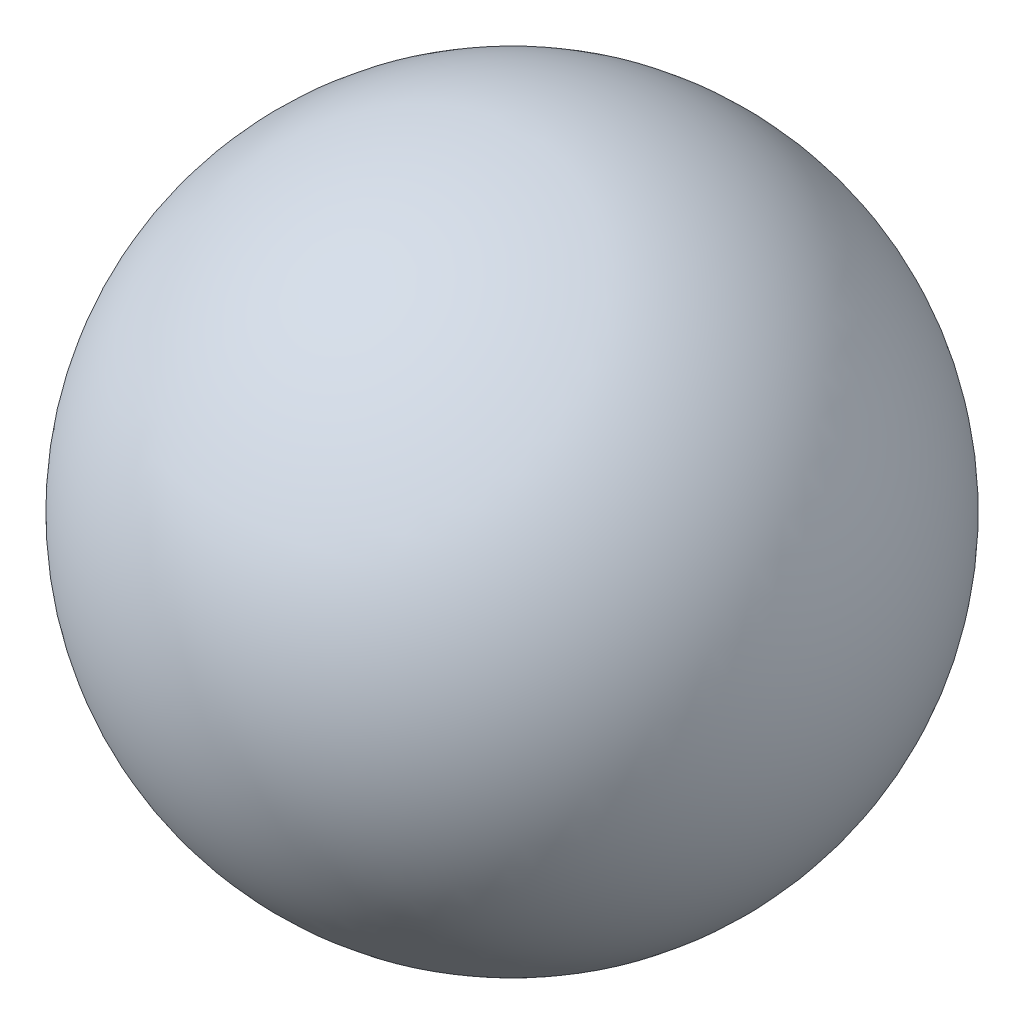
SolidWorks part; units mm, degrees
ref_plane "Front Plane" through (0, 0, 0) normal (0, 0, 1) x (1, 0, 0)
ref_plane "Top Plane" through (0, 0, 0) normal (0, 1, 0) x (1, 0, 0)
ref_plane "Right Plane" through (0, 0, 0) normal (1, 0, 0) x (0, 0, -1)
sketch "Sketch1" plane through (0, 0, 0) normal (0, 0, 1) x (1, 0, 0)
  line L0 (0, 11.25) -> (0, -11.25) construction
  line L1 (0, 11.25) -> (0, -11.25)
  arc A0 (0, 11.25) -> (0, -11.25) centre (0, 0) cw
  dimension "D1" = 11.25
revolve "Revolve1" add sketch "Sketch1" angle 360 about L0
